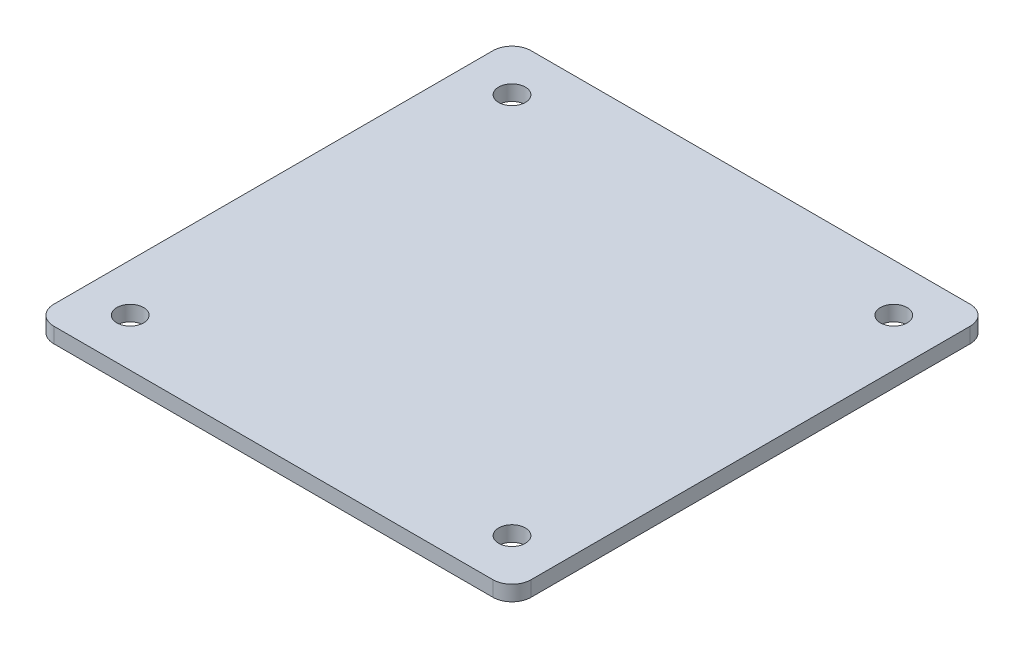
SolidWorks part; units mm, degrees
ref_plane "Plan de face" through (0, 0, 0) normal (0, 0, 1) x (1, 0, 0)
ref_plane "Plan de dessus" through (0, 0, 0) normal (0, 1, 0) x (1, 0, 0)
ref_plane "Plan de droite" through (0, 0, 0) normal (1, 0, 0) x (0, 0, -1)
sketch "Esquisse1" plane through (0, 0, 0) normal (0, 1, 0) x (1, 0, 0)
  line L0 (125, 250) -> (125, 0) construction
  line L1 (10, 0) -> (240, 0)
  line L2 (0, 10) -> (0, 240)
  line L3 (10, 250) -> (240, 250)
  line L4 (250, 10) -> (250, 240)
  line L5 (0, 125) -> (250, 125) construction
  line L6 (0, 25) -> (250, 25) construction
  line L7 (0, 225) -> (250, 225) construction
  line L8 (25, 250) -> (25, 0) construction
  line L9 (225, 250) -> (225, 0) construction
  arc A0 (0, 10) -> (10, 0) centre (10, 10) ccw
  arc A1 (240, 0) -> (250, 10) centre (240, 10) ccw
  arc A2 (250, 240) -> (240, 250) centre (240, 240) ccw
  arc A3 (10, 250) -> (0, 240) centre (10, 240) ccw
  circle A4 centre (25, 225) radius 7
  circle A5 centre (225, 225) radius 7
  circle A6 centre (225, 25) radius 7
  circle A7 centre (25, 25) radius 7
  point P7 (0, 0)
  dimension "D1" = 10
  dimension "D2" = 100
  dimension "D3" = 100
  dimension "D4" = 100
  dimension "D5" = 100
extrude "Boss.-Extru.1" add sketch "Esquisse1" along normal blind 8
sketch "Esquisse2" plane through (0, 8, 0) normal (0, 1, 0) x (-1, 0, 0)
  line L0 (-125, -250) -> (-125, 0) construction
  line L1 (-240, -250) -> (-10, -250) construction
  line L2 (-10, 0) -> (-240, 0) construction
  line L3 (-250, -125) -> (0, -125) construction
  line L4 (0, -240) -> (0, -10) construction
  line L5 (-250, -10) -> (-250, -240) construction
  point P12 (-125, -125)
